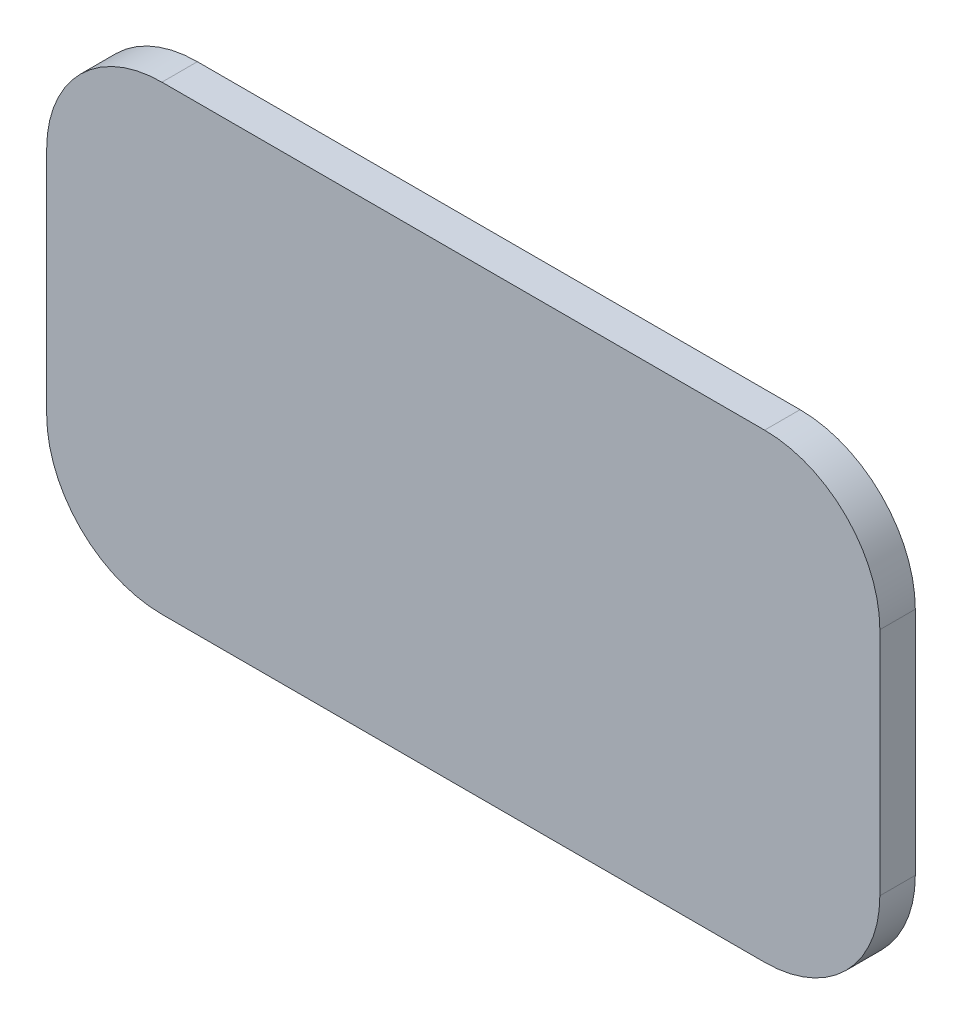
SolidWorks part; units mm, degrees
ref_plane "Спереди" through (0, 0, 0) normal (0, 0, 1) x (1, 0, 0)
ref_plane "Сверху" through (0, 0, 0) normal (0, 1, 0) x (1, 0, 0)
ref_plane "Справа" through (0, 0, 0) normal (1, 0, 0) x (0, 0, -1)
sketch "Эскиз1" plane through (0, 0, 0) normal (0, 0, 1) x (1, 0, 0)
  line L0 (0, 0) -> (0, 50000) construction
  line L1 (-47, -26) -> (47, -26) construction
  line L2 (-47, -26) -> (-47, 26) construction
  line L3 (-47, 26) -> (47, 26) construction
  line L4 (47, -26) -> (47, 26) construction
  line L5 (-47, -26) -> (47, 26) construction
  line L6 (-47, 26) -> (47, -26) construction
  line L7 (0, 0) -> (-50000, 0) construction
  line L8 (-34, 26) -> (34, 26)
  line L9 (47, 13) -> (47, -13)
  line L10 (34, -26) -> (-34, -26)
  line L11 (-47, -13) -> (-47, 13)
  circle A0 centre (-34, 13) radius 13 construction
  circle A1 centre (34, 13) radius 13 construction
  circle A2 centre (34, -13) radius 13 construction
  circle A3 centre (-34, -13) radius 13 construction
  arc A4 (-34, 26) -> (-47, 13) centre (-34, 13) ccw
  arc A5 (-47, -13) -> (-34, -26) centre (-34, -13) ccw
  arc A6 (34, -26) -> (47, -13) centre (34, -13) ccw
  arc A7 (47, 13) -> (34, 26) centre (34, 13) ccw
  point P0 (0, 0)
  dimension "D1" = 94
  dimension "D2" = 52
extrude "Бобышка-Вытянуть1" add sketch "Эскиз1" along normal blind 4
